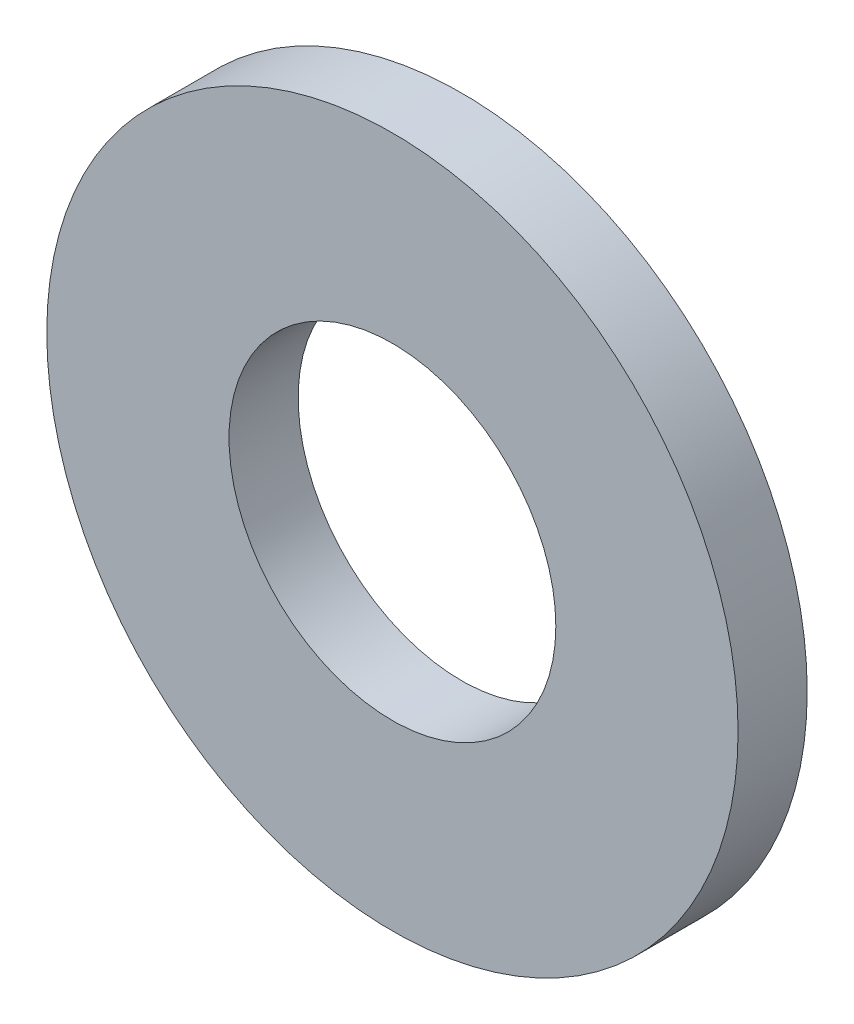
SolidWorks part; units mm, degrees
material "Plain Carbon Steel"
ref_plane "Front Plane" through (0, 0, 0) normal (0, 0, 1) x (1, 0, 0)
ref_plane "Top Plane" through (0, 0, 0) normal (0, 1, 0) x (1, 0, 0)
ref_plane "Right Plane" through (0, 0, 0) normal (1, 0, 0) x (0, 0, -1)
sketch "Sketch1" plane through (0, 0, 0) normal (0, 0, 1) x (1, 0, 0)
  circle A0 centre (0, 0) radius 5.5
  circle A1 centre (0, 0) radius 2.6
  dimension "D1" = 11
  dimension "D2" = 5.2
extrude "Boss-Extrude1" add sketch "Sketch1" along normal blind 1.1
